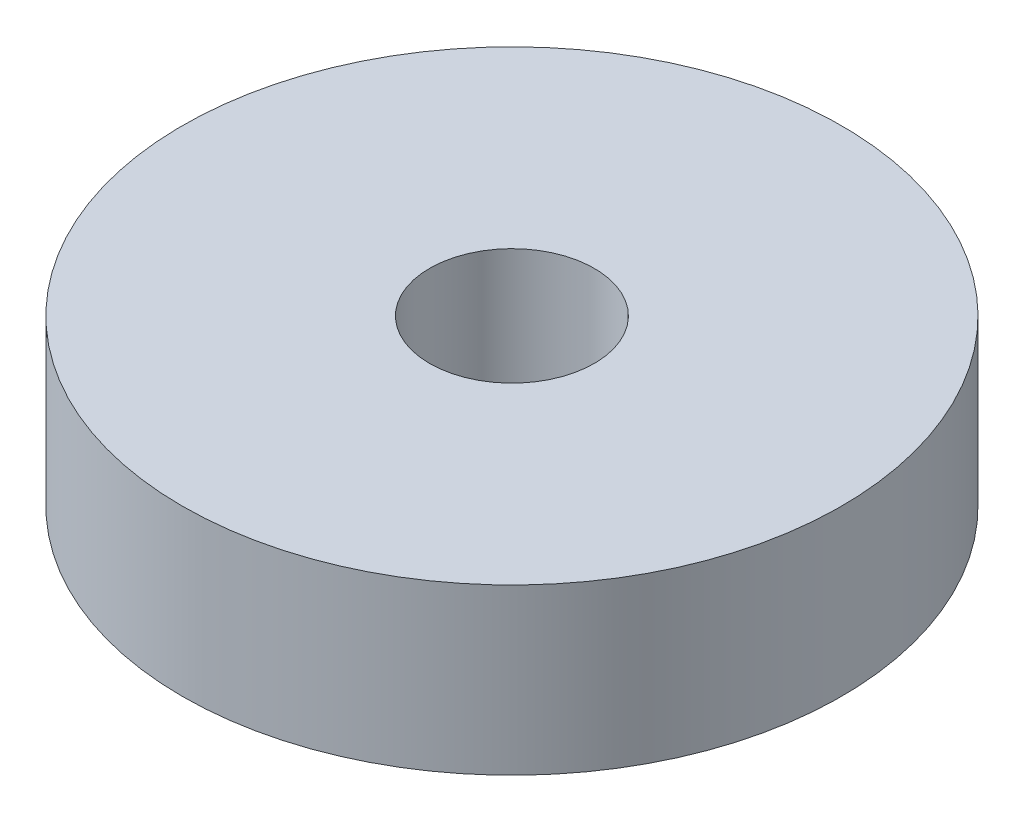
SolidWorks part; units mm, degrees
ref_plane "Front Plane" through (0, 0, 0) normal (0, 0, 1) x (1, 0, 0)
ref_plane "Top Plane" through (0, 0, 0) normal (0, 1, 0) x (1, 0, 0)
ref_plane "Right Plane" through (0, 0, 0) normal (1, 0, 0) x (0, 0, -1)
sketch "Sketch1" plane through (0, 0, 0) normal (0, 1, 0) x (1, 0, 0)
  circle A0 centre (0, 0) radius 1.5
  circle A1 centre (0, 0) radius 6
  dimension "D1" = 3
  dimension "D2" = 12
extrude "Boss-Extrude1" add sketch "Sketch1" along normal blind 3
